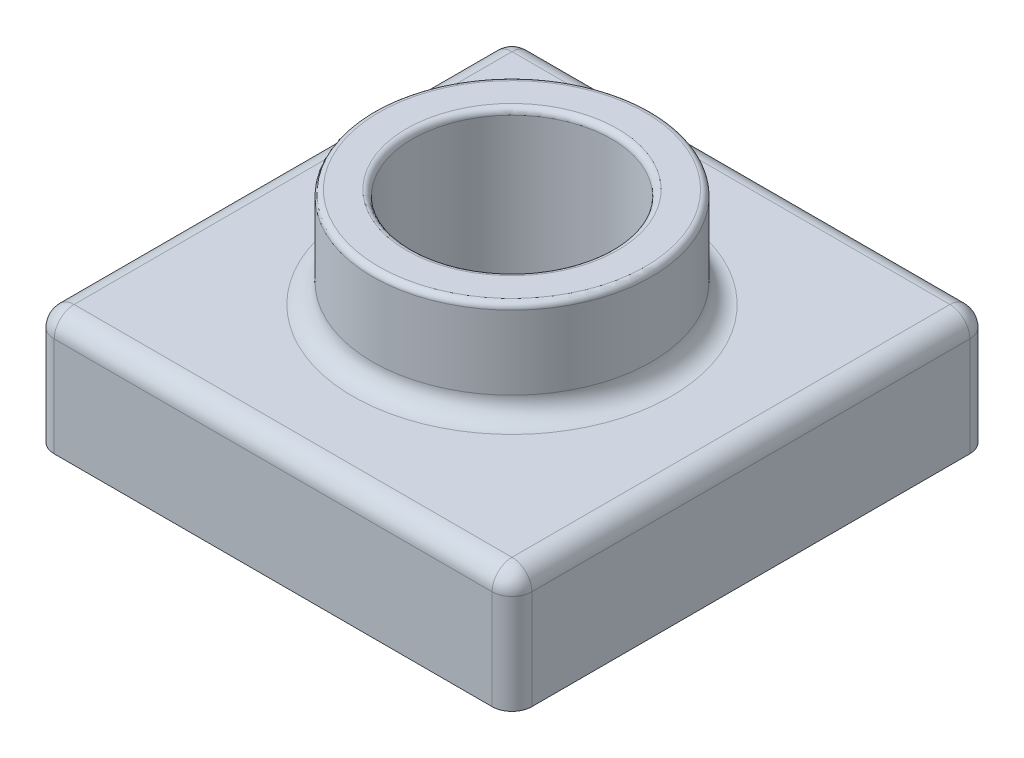
SolidWorks part; units mm, degrees
ref_plane "Front Plane" through (0, 0, 0) normal (0, 0, 1) x (1, 0, 0)
ref_plane "Top Plane" through (0, 0, 0) normal (0, 1, 0) x (1, 0, 0)
ref_plane "Right Plane" through (0, 0, 0) normal (1, 0, 0) x (0, 0, -1)
sketch "Sketch2" plane through (0, 0, 0) normal (0, 1, 0) x (1, 0, 0)
  line L1 (0, 0) -> (120, 0)
  line L2 (0, 0) -> (0, 120)
  line L3 (0, 120) -> (120, 120)
  line L4 (120, 0) -> (120, 120)
  dimension "D1" = 120
  dimension "D2" = 120
extrude "Boss-Extrude1" add sketch "Sketch2" along normal blind 30
sketch "Sketch4" plane through (0, 30, 0) normal (0, 1, 0) x (1, 0, 0)
  line L0 (120, 120) -> (0, 120) construction
  line L1 (0, 120) -> (0, 0) construction
  circle A0 centre (60, 60) radius 35
  dimension "D1" = 70
  dimension "D2" = 60
  dimension "D3" = 60
extrude "Boss-Extrude2" add sketch "Sketch4" along normal blind 25
sketch "Sketch5" plane through (0, 55, 0) normal (0, 1, 0) x (1, 0, 0)
  line L0 (0, 120) -> (0, 0) construction
  line L1 (120, 120) -> (0, 120) construction
  circle A0 centre (60, 60) radius 25
  circle A1 centre (60, 60) radius 35 construction
  point P4 (0, 60)
  dimension "D3" = 10
  dimension "D1" = 60
  dimension "D2" = 60
extrude "Cut-Extrude1" cut sketch "Sketch5" against normal through all and the other way through all
fillet "Fillet1" radius 5 9 edges at (60, 30, -120) (120, 30, -60) (60, 30, 0) (0, 30, -60) (60, 30, -25) (0, 15, -120) (120, 15, -120) (120, 15, 0) (0, 15, 0)
fillet "Fillet2" radius 1.5 2 edges at (60, 55, -25) (60, 55, -35)
shell "Shell1" thickness 2
